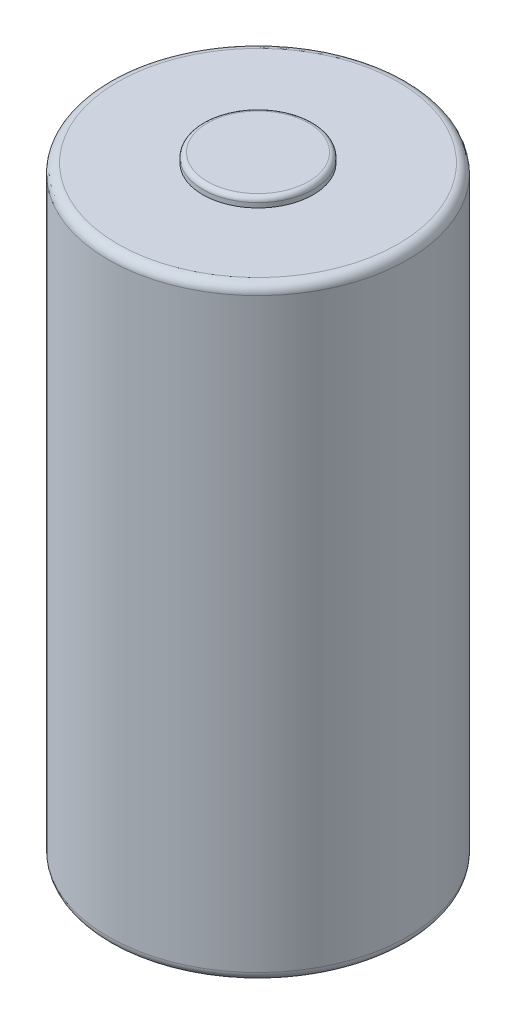
SolidWorks part; units mm, degrees
ref_plane "Front Plane" through (0, 0, 0) normal (0, 0, 1) x (1, 0, 0)
ref_plane "Top Plane" through (0, 0, 0) normal (0, 1, 0) x (1, 0, 0)
ref_plane "Right Plane" through (0, 0, 0) normal (1, 0, 0) x (0, 0, -1)
sketch "Sketch1" plane through (0, 0, 0) normal (0, 1, 0) x (1, 0, 0)
  circle A0 centre (0, 0) radius 8.255
  dimension "D1" = 16.51
extrude "Boss-Extrude1" add sketch "Sketch1" along normal blind 33.3756
sketch "Sketch2" plane through (0, 33.3756, 0) normal (0, 1, 0) x (1, 0, 0)
  circle A0 centre (0, 0) radius 3.048
  dimension "D1" = 6.096
extrude "Boss-Extrude2" add sketch "Sketch2" along normal blind 0.508
sketch "Sketch3" plane through (0, 0, 0) normal (0, -1, 0) x (1, 0, 0)
  circle A0 centre (0, 0) radius 5.08
  dimension "D1" = 10.16
extrude "Boss-Extrude3" add sketch "Sketch3" along normal blind 0.1016
fillet "Fillet1" radius 0.508 2 edges at (0, 33.3756, 8.255) (0, 0, 8.255)
fillet "Fillet2" radius 0.254 1 edges at (0, 33.8836, 3.048)
